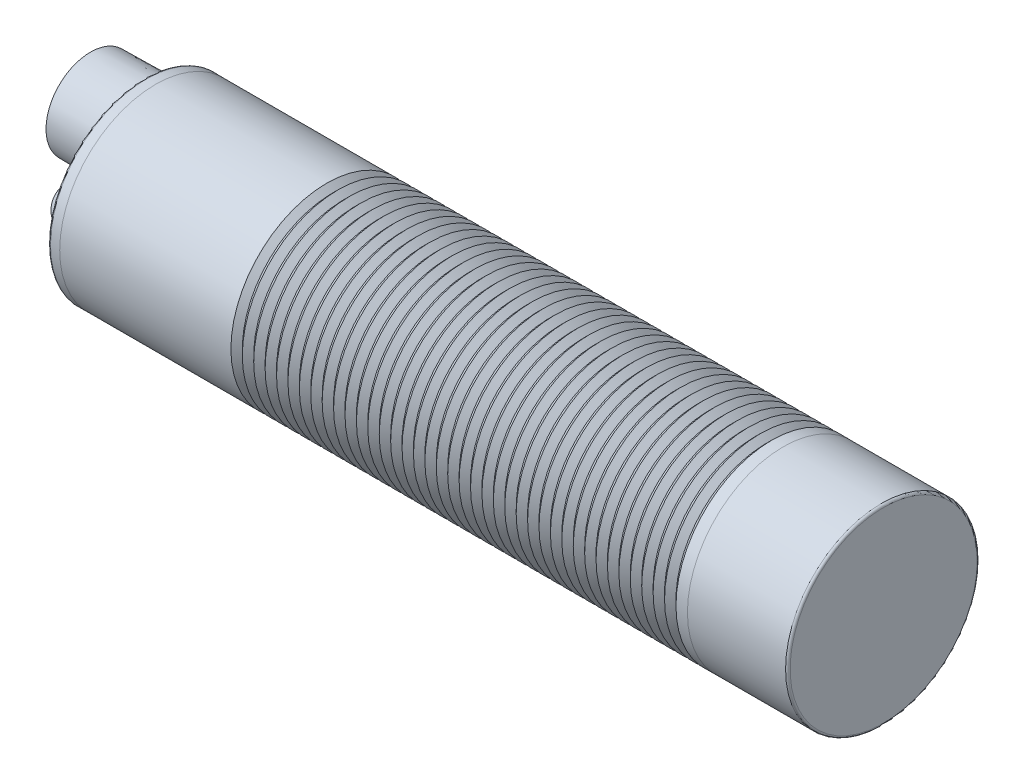
SolidWorks part; units mm, degrees
ref_plane "Front Plane" through (0, 0, 0) normal (0, 0, 1) x (1, 0, 0)
ref_plane "Top Plane" through (0, 0, 0) normal (0, 1, 0) x (1, 0, 0)
ref_plane "Right Plane" through (0, 0, 0) normal (1, 0, 0) x (0, 0, -1)
sketch "Sketch1" plane through (0, 0, 0) normal (1, 0, 0) x (0, 0, -1)
  circle A0 centre (0, 0) radius 8.4
  dimension "D1" = 16.8
extrude "Boss-Extrude1" add sketch "Sketch1" along normal blind 1
sketch "Sketch2" plane through (1, 0, 0) normal (1, 0, 0) x (0, 0, -1)
  circle A0 centre (0, 0) radius 8.395
  dimension "D1" = 16.79
extrude "Boss-Extrude2" add sketch "Sketch2" along normal blind 55
sketch "Sketch3" plane through (56, 0, 0) normal (1, 0, 0) x (0, 0, -1)
  circle A0 centre (0, 0) radius 8.39
  dimension "D1" = 16.78
extrude "Boss-Extrude3" add sketch "Sketch3" along normal blind 8.8
sketch "Sketch4" plane through (0, 0, 0) normal (0, 0, 1) x (1, 0, 0)
  line L0 (16, 8.395) -> (56, 8.395)
  line L1 (56, 8.395) -> (1, 8.395) construction
  line L2 (1, 10.4936) -> (1, 5.0865) construction
  line L4 (16, 8.395) -> (16.5, 7.895)
  line L5 (16.5, 7.895) -> (17, 8.395)
  line L6 (17.5, 7.895) -> (18, 8.395)
  line L7 (17, 8.395) -> (17.5, 7.895)
  line L8 (18.5, 7.895) -> (19, 8.395)
  line L9 (18, 8.395) -> (18.5, 7.895)
  line L10 (19.5, 7.895) -> (20, 8.395)
  line L11 (19, 8.395) -> (19.5, 7.895)
  line L12 (20.5, 7.895) -> (21, 8.395)
  line L13 (20, 8.395) -> (20.5, 7.895)
  line L14 (21.5, 7.895) -> (22, 8.395)
  line L15 (21, 8.395) -> (21.5, 7.895)
  line L16 (22.5, 7.895) -> (23, 8.395)
  line L17 (22, 8.395) -> (22.5, 7.895)
  line L18 (23.5, 7.895) -> (24, 8.395)
  line L19 (23, 8.395) -> (23.5, 7.895)
  line L20 (24.5, 7.895) -> (25, 8.395)
  line L21 (24, 8.395) -> (24.5, 7.895)
  line L22 (25.5, 7.895) -> (26, 8.395)
  line L23 (25, 8.395) -> (25.5, 7.895)
  line L24 (26.5, 7.895) -> (27, 8.395)
  line L25 (26, 8.395) -> (26.5, 7.895)
  line L26 (27.5, 7.895) -> (28, 8.395)
  line L27 (27, 8.395) -> (27.5, 7.895)
  line L28 (28.5, 7.895) -> (29, 8.395)
  line L29 (28, 8.395) -> (28.5, 7.895)
  line L30 (29.5, 7.895) -> (30, 8.395)
  line L31 (29, 8.395) -> (29.5, 7.895)
  line L32 (30.5, 7.895) -> (31, 8.395)
  line L33 (30, 8.395) -> (30.5, 7.895)
  line L34 (31.5, 7.895) -> (32, 8.395)
  line L35 (31, 8.395) -> (31.5, 7.895)
  line L36 (32.5, 7.895) -> (33, 8.395)
  line L37 (32, 8.395) -> (32.5, 7.895)
  line L38 (33.5, 7.895) -> (34, 8.395)
  line L39 (33, 8.395) -> (33.5, 7.895)
  line L40 (34.5, 7.895) -> (35, 8.395)
  line L41 (34, 8.395) -> (34.5, 7.895)
  line L42 (35.5, 7.895) -> (36, 8.395)
  line L43 (35, 8.395) -> (35.5, 7.895)
  line L44 (36.5, 7.895) -> (37, 8.395)
  line L45 (36, 8.395) -> (36.5, 7.895)
  line L46 (37.5, 7.895) -> (38, 8.395)
  line L47 (37, 8.395) -> (37.5, 7.895)
  line L48 (38.5, 7.895) -> (39, 8.395)
  line L49 (38, 8.395) -> (38.5, 7.895)
  line L50 (39.5, 7.895) -> (40, 8.395)
  line L51 (39, 8.395) -> (39.5, 7.895)
  line L52 (40.5, 7.895) -> (41, 8.395)
  line L53 (40, 8.395) -> (40.5, 7.895)
  line L54 (41.5, 7.895) -> (42, 8.395)
  line L55 (41, 8.395) -> (41.5, 7.895)
  line L56 (42.5, 7.895) -> (43, 8.395)
  line L57 (42, 8.395) -> (42.5, 7.895)
  line L58 (43.5, 7.895) -> (44, 8.395)
  line L59 (43, 8.395) -> (43.5, 7.895)
  line L60 (44.5, 7.895) -> (45, 8.395)
  line L61 (44, 8.395) -> (44.5, 7.895)
  line L62 (45.5, 7.895) -> (46, 8.395)
  line L63 (45, 8.395) -> (45.5, 7.895)
  line L64 (46.5, 7.895) -> (47, 8.395)
  line L65 (46, 8.395) -> (46.5, 7.895)
  line L66 (47.5, 7.895) -> (48, 8.395)
  line L67 (47, 8.395) -> (47.5, 7.895)
  line L68 (48.5, 7.895) -> (49, 8.395)
  line L69 (48, 8.395) -> (48.5, 7.895)
  line L70 (49.5, 7.895) -> (50, 8.395)
  line L71 (49, 8.395) -> (49.5, 7.895)
  line L72 (50.5, 7.895) -> (51, 8.395)
  line L73 (50, 8.395) -> (50.5, 7.895)
  line L74 (51.5, 7.895) -> (52, 8.395)
  line L75 (51, 8.395) -> (51.5, 7.895)
  line L76 (52.5, 7.895) -> (53, 8.395)
  line L77 (52, 8.395) -> (52.5, 7.895)
  line L78 (53.5, 7.895) -> (54, 8.395)
  line L79 (53, 8.395) -> (53.5, 7.895)
  line L80 (54.5, 7.895) -> (55, 8.395)
  line L81 (54, 8.395) -> (54.5, 7.895)
  dimension "D2" = 45
  dimension "D3" = 1
  dimension "D4" = 20
  dimension "D5" = 20
revolve "Cut-Revolve1" cut sketch "Sketch4" angle 360 about axis through (56, 0, 0) along (-1, 0, 0)
sketch "Sketch5" plane through (0, 0, 0) normal (-1, 0, 0) x (0, 0, 1)
  line L0 (-9.9612, 0) -> (9.2306, 0) construction
  line L1 (0, 9.1589) -> (0, -10.1785) construction
  circle A0 centre (-4.1, 0) radius 4.05
  circle A1 centre (-4.1, 0) radius 3.5
  dimension "D1" = 8.1
  dimension "D3" = 7
  dimension "D2" = 4.1
extrude "Boss-Extrude4" add sketch "Sketch5" along normal blind 8.8 draft 1
sketch "Sketch6" plane through (0, 0, 0) normal (-1, 0, 0) x (0, 0, 1)
  circle A0 centre (4.3355, 0) radius 2
  dimension "D1" = 4
extrude "Boss-Extrude5" add sketch "Sketch6" along normal blind 3
fillet "Fillet1" radius 2 1 edges at (-3, 0, 6.3355)
fillet "Fillet2" radius 0.2 1 edges at (64.8, 0, -8.39)
fillet "Fillet3" radius 0.2 1 edges at (0, 0, -8.4)
fillet "Fillet4" radius 0.2 2 edges at (0, 0, 2.3355) (0, 0, -8.15)
